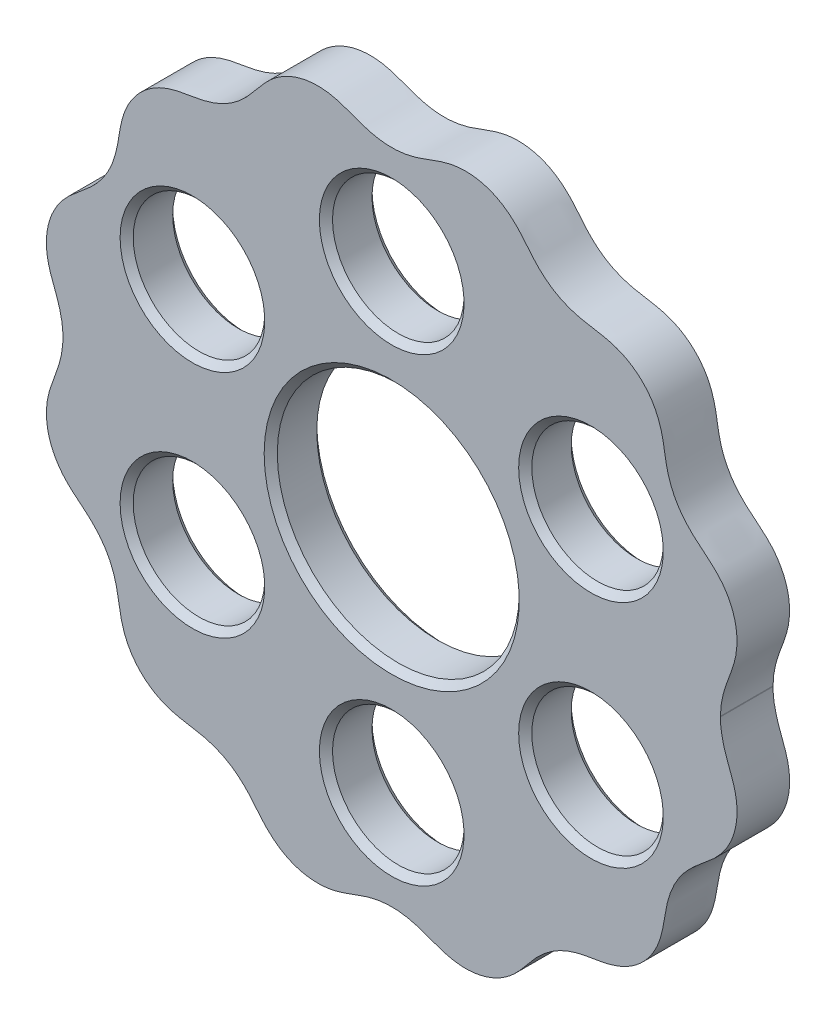
SolidWorks part; units mm, degrees
material "Polylactic Acid (PLA)"
ref_plane "Front Plane" through (0, 0, 0) normal (0, 0, 1) x (1, 0, 0)
ref_plane "Top Plane" through (0, 0, 0) normal (0, 1, 0) x (1, 0, 0)
ref_plane "Right Plane" through (0, 0, 0) normal (1, 0, 0) x (0, 0, -1)
sketch "Sketch3" plane through (0, 0, 0) normal (0, 0, 1) x (1, 0, 0)
  circle A0 centre (0, 0) radius 9.2
  circle A1 centre (0, 0) radius 17.5 construction
  circle A2 centre (0, 17.5) radius 5
  circle A3 centre (15.1554, 8.75) radius 5
  circle A4 centre (15.1554, -8.75) radius 5
  circle A5 centre (0, -17.5) radius 5
  circle A6 centre (-15.1554, -8.75) radius 5
  circle A7 centre (-15.1554, 8.75) radius 5
  spline S0 degree 4 poles (21.1908, 13.4898) (21.2856, 13.2293) (21.5047, 12.7166) (21.9256, 11.9944) (22.6531, 11.1441) (23.6487, 10.2926) (24.8547, 9.373) (25.8136, 8.0448) (26.2513, 6.5807) (26.291, 5.362) (26.1425, 4.3728) (25.9222, 3.637) (25.662, 2.971) (25.4535, 2.4089) (25.3271, 2.03) (25.2348, 1.7101) (25.1694, 1.4518) (25.1138, 1.1915) (25.0684, 0.9287) (25.0339, 0.6638) (25.0136, 0.4392) (25.0034, 0.2182) (24.9998, 0.0511) (24.9998, -0.0519) (25.0027, -0.1861) (25.0086, -0.3317) (25.0175, -0.4711) (25.0292, -0.6041) (25.0438, -0.7358) (25.0613, -0.8682) (25.0866, -1.0342) (25.1223, -1.2324) (25.1717, -1.4616) (25.2379, -1.7216) (25.3315, -2.0435) (25.4377, -2.3615) (25.5528, -2.6764) (25.6953, -3.0525) (25.8373, -3.4288) (26.0075, -3.9196) (26.1691, -4.5364) (26.293, -5.4006) (26.2489, -6.5093) (25.9006, -7.7589) (25.2509, -8.824) (24.5594, -9.5488) (23.8729, -10.1329) (23.242, -10.6335) (22.5405, -11.262) (21.8598, -12.0935) (21.3371, -13.0271) (20.9865, -14.0322) (20.7832, -15.0691) (20.6292, -16.2106) (20.2958, -17.4236) (19.6201, -18.6144) (18.5782, -19.6482) (17.3773, -20.3163) (16.1515, -20.64) (14.7399, -20.8265) (13.4394, -21.1259) (12.2371, -21.7311) (11.2173, -22.5863) (10.5105, -23.3824) (9.8039, -24.3012) (8.9125, -25.2023) (7.7314, -25.9117) (6.3093, -26.2999) (4.9316, -26.2885) (3.7061, -25.9646) (2.6337, -25.523) (1.6267, -25.1818) (0.5814, -24.9891) (-0.4789, -24.9807) (-1.521, -25.1546) (-2.5204, -25.4795) (-3.4192, -25.8479) (-4.2744, -26.1194) (-5.0841, -26.2552) (-5.8272, -26.2778) (-6.7511, -26.1767) (-7.8194, -25.8504) (-8.8645, -25.242) (-9.7745, -24.3376) (-10.489, -23.4094) (-11.1981, -22.6045) (-12.0193, -21.9108) (-12.9507, -21.3713) (-13.9612, -21.0044) (-15.0125, -20.7907) (-16.1735, -20.6366) (-17.4128, -20.3041) (-18.6216, -19.6172) (-19.5352, -18.6909) (-20.1095, -17.7445) (-20.4683, -16.8114) (-20.6693, -15.9295) (-20.8004, -14.9513) (-21.0215, -13.8975) (-21.3995, -12.8918) (-21.9457, -11.9715) (-22.6396, -11.1645) (-23.4354, -10.4692) (-24.3471, -9.7654) (-25.2322, -8.8715) (-25.9257, -7.6947) (-26.3017, -6.2829) (-26.2854, -4.917) (-25.9623, -3.7014) (-25.5242, -2.6362) (-25.1845, -1.6355) (-24.9896, -0.5891) (-24.9797, 0.481) (-25.1578, 1.5405) (-25.4952, 2.5629) (-25.8707, 3.4757) (-26.1355, 4.3406) (-26.2885, 5.3286) (-26.2611, 6.43) (-25.9336, 7.6784) (-25.2377, 8.8666) (-24.345, 9.7676) (-23.427, 10.4756) (-22.627, 11.1764) (-21.9369, 11.9843) (-21.3977, 12.8977) (-21.0267, 13.8865) (-20.8061, 14.9146) (-20.653, 16.0603) (-20.3956, 17.1161) (-19.9569, 18.0284) (-19.3001, 18.9288) (-18.4837, 19.6923) (-17.4358, 20.2946) (-16.1976, 20.6324) (-15.0368, 20.7873) (-13.9849, 20.9979) (-12.9731, 21.361) (-12.0395, 21.8966) (-11.2157, 22.5872) (-10.504, 23.3902) (-9.7903, 24.3186) (-8.8841, 25.2269) (-7.6859, 25.9322) (-6.4273, 26.2622) (-5.3206, 26.2881) (-4.3329, 26.1336) (-3.4683, 25.8679) (-2.5556, 25.4923) (-1.5328, 25.1559) (-0.4731, 24.979) (0.597, 24.9904) (1.6431, 25.1866) (2.6435, 25.5272) (3.7088, 25.9651) (4.9249, 26.2864) (6.2909, 26.3007) (7.702, 25.9226) (8.8779, 25.2273) (9.7704, 24.341) (10.4741, 23.4292) (11.1701, 22.634) (11.978, 21.941) (12.899, 21.3961) (13.9051, 21.0193) (14.9591, 20.7992) (15.9373, 20.6681) (16.819, 20.466) (17.7516, 20.1059) (18.6971, 19.5302) (19.6221, 18.6152) (20.3072, 17.4054) (20.6379, 16.1657) (20.7918, 15.0047) (21.0066, 13.9535) (21.3747, 12.9435) (21.9154, 12.0128) (22.6101, 11.1925) (23.4156, 10.4841) (24.3437, 9.7696) (25.2468, 8.858) (25.9409, 7.6621) (26.2625, 6.4138) (26.2848, 5.4123) (26.1914, 4.7043) (26.0881, 4.2266) (25.9672, 3.8023) (25.8079, 3.3457) (25.6196, 2.8553) (25.4588, 2.4245) (25.3339, 2.0507) (25.2417, 1.7354) (25.1764, 1.4809) (25.1203, 1.2244) (25.0741, 0.9651) (25.0385, 0.7047) (25.017, 0.4825) (25.0053, 0.2643) (25.0004, 0.1004) (24.9996, -0.0012) (25.0018, -0.1656) (25.01, -0.3844) (25.028, -0.6072) (25.0597, -0.8689) (25.1021, -1.1294) (25.1679, -1.4517) (25.266, -1.8346) (25.4047, -2.2742) (25.5863, -2.7686) (25.7756, -3.26) (25.9402, -3.7196) (26.0686, -4.1508) (26.1813, -4.6424) (26.2599, -5.1966) (26.2771, -5.8503) (26.1868, -6.6388) (25.9656, -7.4497) (25.5952, -8.2566) (25.0637, -9.0243) (24.3767, -9.7304) (23.5662, -10.3704) (22.7327, -11.0654) (21.9759, -11.9212) (21.5356, -12.6558) (21.307, -13.1772) (21.208, -13.4432) knots 0 0 0 0 0 0.005467 0.010935 0.016402 0.021869 0.031276 0.040682 0.047884 0.051484 0.055085 0.060328 0.062949 0.065571 0.066882 0.068192 0.069503 0.070814 0.072125 0.073435 0.074746 0.075401 0.076057 0.076717 0.077377 0.078036 0.078696 0.079356 0.080016 0.080676 0.081336 0.082656 0.083975 0.085295 0.086615 0.089254 0.090574 0.091894 0.094534 0.097173 0.100798 0.104424 0.111675 0.118848 0.126022 0.128665 0.131308 0.136594 0.14188 0.147166 0.152358 0.157549 0.16274 0.167931 0.175042 0.182153 0.189327 0.1965 0.201723 0.206946 0.217392 0.222615 0.227838 0.233061 0.238284 0.245457 0.252631 0.259805 0.266978 0.272201 0.277424 0.282647 0.287869 0.29303 0.29819 0.30335 0.30851 0.31216 0.31581 0.319459 0.323109 0.330383 0.337658 0.342925 0.348192 0.35346 0.358727 0.363994 0.369262 0.374529 0.379796 0.387071 0.394345 0.401519 0.405106 0.408692 0.413978 0.419265 0.424551 0.429837 0.435028 0.440219 0.44541 0.450602 0.457712 0.464823 0.471934 0.479045 0.484236 0.489427 0.494619 0.49981 0.505096 0.510382 0.515668 0.520954 0.524541 0.528128 0.535301 0.542475 0.549649 0.554872 0.560094 0.565317 0.57054 0.5757 0.58086 0.58602 0.591181 0.59848 0.60213 0.605779 0.613054 0.620328 0.625595 0.630863 0.63613 0.641397 0.646665 0.651932 0.657199 0.662467 0.669741 0.677015 0.684189 0.687776 0.691363 0.696649 0.701935 0.707221 0.712507 0.717698 0.722889 0.728081 0.733272 0.740383 0.747494 0.754604 0.761715 0.766906 0.772098 0.777289 0.78248 0.787766 0.793052 0.798338 0.803624 0.807211 0.810798 0.817972 0.825246 0.83252 0.837788 0.843055 0.848322 0.85359 0.858857 0.864124 0.869392 0.874659 0.881933 0.889208 0.896232 0.899744 0.9015 0.903256 0.905842 0.908428 0.911014 0.9136 0.914893 0.916186 0.917479 0.918772 0.920065 0.921358 0.922651 0.923297 0.923944 0.924592 0.92524 0.926536 0.927831 0.929127 0.930423 0.931719 0.934311 0.936903 0.939495 0.942087 0.944679 0.946512 0.948345 0.952012 0.955678 0.959345 0.963918 0.968492 0.973065 0.977639 0.983229 0.988819 0.99441 1 1 1 1 1 construction
  spline S1 degree 4 poles (25, 0) (25, -0.0284) (25.0005, -0.0852) (25.0027, -0.1861) (25.0086, -0.3317) (25.0175, -0.4711) (25.0292, -0.6041) (25.0438, -0.7358) (25.0613, -0.8682) (25.0866, -1.0342) (25.1223, -1.2324) (25.1717, -1.4616) (25.2379, -1.7216) (25.3315, -2.0435) (25.4377, -2.3615) (25.5528, -2.6764) (25.6953, -3.0525) (25.8373, -3.4288) (26.0075, -3.9196) (26.1691, -4.5364) (26.293, -5.4006) (26.2489, -6.5093) (25.9006, -7.7589) (25.2509, -8.824) (24.5594, -9.5488) (23.8729, -10.1329) (23.242, -10.6335) (22.5405, -11.262) (21.8598, -12.0935) (21.3371, -13.0271) (20.9865, -14.0322) (20.7832, -15.0691) (20.6292, -16.2106) (20.2958, -17.4236) (19.6201, -18.6144) (18.5782, -19.6482) (17.3773, -20.3163) (16.1515, -20.64) (14.7399, -20.8265) (13.4394, -21.1259) (12.2371, -21.7311) (11.2173, -22.5863) (10.5105, -23.3824) (9.8039, -24.3012) (8.9125, -25.2023) (7.7314, -25.9117) (6.3093, -26.2999) (4.9316, -26.2885) (3.7061, -25.9646) (2.6337, -25.523) (1.6267, -25.1818) (0.5814, -24.9891) (-0.4789, -24.9807) (-1.521, -25.1546) (-2.5204, -25.4795) (-3.4192, -25.8479) (-4.2744, -26.1194) (-5.0841, -26.2552) (-5.8272, -26.2778) (-6.7511, -26.1767) (-7.8194, -25.8504) (-8.8645, -25.242) (-9.7745, -24.3376) (-10.489, -23.4094) (-11.1981, -22.6045) (-12.0193, -21.9108) (-12.9507, -21.3713) (-13.9612, -21.0044) (-15.0125, -20.7907) (-16.1735, -20.6366) (-17.4128, -20.3041) (-18.6216, -19.6172) (-19.5352, -18.6909) (-20.1095, -17.7445) (-20.4683, -16.8114) (-20.6693, -15.9295) (-20.8004, -14.9513) (-21.0215, -13.8975) (-21.3995, -12.8918) (-21.9457, -11.9715) (-22.6396, -11.1645) (-23.4354, -10.4692) (-24.3471, -9.7654) (-25.2322, -8.8715) (-25.9257, -7.6947) (-26.3017, -6.2829) (-26.2854, -4.917) (-25.9623, -3.7014) (-25.5242, -2.6362) (-25.1845, -1.6355) (-24.9896, -0.5891) (-24.9797, 0.481) (-25.1578, 1.5405) (-25.4952, 2.5629) (-25.8707, 3.4757) (-26.1355, 4.3406) (-26.2885, 5.3286) (-26.2611, 6.43) (-25.9336, 7.6784) (-25.2377, 8.8666) (-24.345, 9.7676) (-23.427, 10.4756) (-22.627, 11.1764) (-21.9369, 11.9843) (-21.3977, 12.8977) (-21.0267, 13.8865) (-20.8061, 14.9146) (-20.653, 16.0603) (-20.3956, 17.1161) (-19.9569, 18.0284) (-19.3001, 18.9288) (-18.4837, 19.6923) (-17.4358, 20.2946) (-16.1976, 20.6324) (-15.0368, 20.7873) (-13.9849, 20.9979) (-12.9731, 21.361) (-12.0395, 21.8966) (-11.2157, 22.5872) (-10.504, 23.3902) (-9.7903, 24.3186) (-8.8841, 25.2269) (-7.6859, 25.9322) (-6.4273, 26.2622) (-5.3206, 26.2881) (-4.3329, 26.1336) (-3.4683, 25.8679) (-2.5556, 25.4923) (-1.5328, 25.1559) (-0.4731, 24.979) (0.597, 24.9904) (1.6431, 25.1866) (2.6435, 25.5272) (3.7088, 25.9651) (4.9249, 26.2864) (6.2909, 26.3007) (7.702, 25.9226) (8.8779, 25.2273) (9.7704, 24.341) (10.4741, 23.4292) (11.1701, 22.634) (11.978, 21.941) (12.899, 21.3961) (13.9051, 21.0193) (14.9591, 20.7992) (15.9373, 20.6681) (16.819, 20.466) (17.7516, 20.1059) (18.6971, 19.5302) (19.6221, 18.6152) (20.3072, 17.4054) (20.6379, 16.1657) (20.7918, 15.0047) (21.0066, 13.9535) (21.3747, 12.9435) (21.9154, 12.0128) (22.6101, 11.1925) (23.4156, 10.4841) (24.3437, 9.7696) (25.2468, 8.858) (25.9409, 7.6621) (26.2625, 6.4138) (26.2848, 5.4123) (26.1914, 4.7043) (26.0881, 4.2266) (25.9672, 3.8023) (25.8079, 3.3457) (25.6196, 2.8553) (25.4588, 2.4245) (25.3339, 2.0507) (25.2417, 1.7354) (25.1764, 1.4809) (25.1203, 1.2244) (25.0741, 0.9651) (25.0385, 0.7047) (25.017, 0.4825) (25.0053, 0.2643) (25.0014, 0.1332) (25.0004, 0.0775) (25.0002, 0.0497) knots 0.076057 0.076057 0.076057 0.076057 0.076057 0.076717 0.077377 0.078036 0.078696 0.079356 0.080016 0.080676 0.081336 0.082656 0.083975 0.085295 0.086615 0.089254 0.090574 0.091894 0.094534 0.097173 0.100798 0.104424 0.111675 0.118848 0.126022 0.128665 0.131308 0.136594 0.14188 0.147166 0.152358 0.157549 0.16274 0.167931 0.175042 0.182153 0.189327 0.1965 0.201723 0.206946 0.217392 0.222615 0.227838 0.233061 0.238284 0.245457 0.252631 0.259805 0.266978 0.272201 0.277424 0.282647 0.287869 0.29303 0.29819 0.30335 0.30851 0.31216 0.31581 0.319459 0.323109 0.330383 0.337658 0.342925 0.348192 0.35346 0.358727 0.363994 0.369262 0.374529 0.379796 0.387071 0.394345 0.401519 0.405106 0.408692 0.413978 0.419265 0.424551 0.429837 0.435028 0.440219 0.44541 0.450602 0.457712 0.464823 0.471934 0.479045 0.484236 0.489427 0.494619 0.49981 0.505096 0.510382 0.515668 0.520954 0.524541 0.528128 0.535301 0.542475 0.549649 0.554872 0.560094 0.565317 0.57054 0.5757 0.58086 0.58602 0.591181 0.59848 0.60213 0.605779 0.613054 0.620328 0.625595 0.630863 0.63613 0.641397 0.646665 0.651932 0.657199 0.662467 0.669741 0.677015 0.684189 0.687776 0.691363 0.696649 0.701935 0.707221 0.712507 0.717698 0.722889 0.728081 0.733272 0.740383 0.747494 0.754604 0.761715 0.766906 0.772098 0.777289 0.78248 0.787766 0.793052 0.798338 0.803624 0.807211 0.810798 0.817972 0.825246 0.83252 0.837788 0.843055 0.848322 0.85359 0.858857 0.864124 0.869392 0.874659 0.881933 0.889208 0.896232 0.899744 0.9015 0.903256 0.905842 0.908428 0.911014 0.9136 0.914893 0.916186 0.917479 0.918772 0.920065 0.921358 0.922651 0.923297 0.923944 0.923944 0.923944 0.923944 0.923944
  spline S2 degree 1 poles (25.0002, 0.0497) (25, 0) knots 0 0 1 1
  point P17 (0, 0)
  dimension "D1" = 18.4
  dimension "D2" = 35
  dimension "D3" = 10
  dimension "D4" = 6
extrude "Boss-Extrude2" add sketch "Sketch3" along normal blind 4
chamfer "Chamfer1" distance 0.5 angle 45 14 edges at (-10.1554, 8.75, 0) (-10.1554, 8.75, 4) (5, 17.5, 0) (5, 17.5, 4) (20.1554, 8.75, 0) (20.1554, 8.75, 4) (20.1554, -8.75, 0) (20.1554, -8.75, 4) (5, -17.5, 0) (5, -17.5, 4) (-10.1554, -8.75, 0) (-10.1554, -8.75, 4) (9.2, 0, 0) (9.2, 0, 4)
